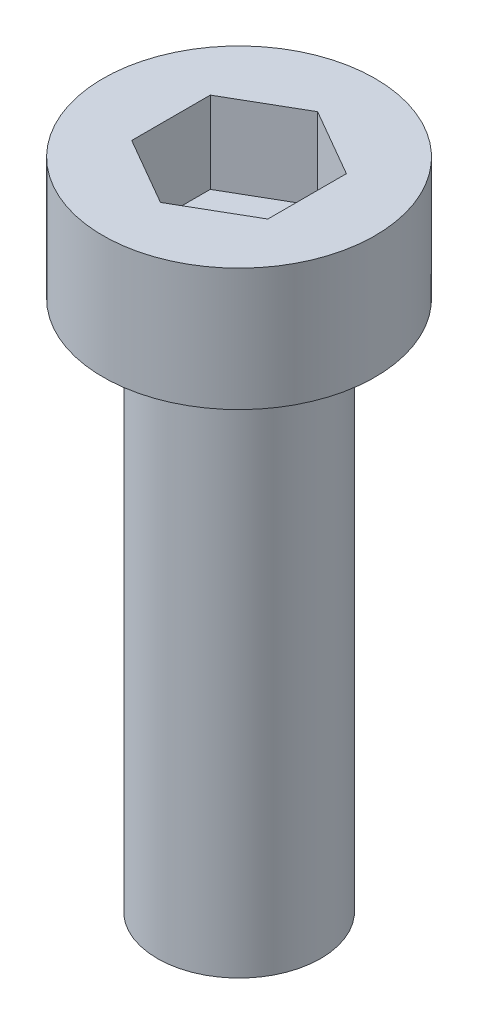
SolidWorks part; units mm, degrees
material "AISI 4340 Stal normalizowana"
ref_plane "Płaszczyzna XY" through (0, 0, 0) normal (0, 0, 1) x (1, 0, 0)
ref_plane "Płaszczyzna XZ" through (0, 0, 0) normal (0, 1, 0) x (1, 0, 0)
ref_plane "Płaszczyzna YZ" through (0, 0, 0) normal (1, 0, 0) x (0, 0, -1)
sketch "Szkic1" plane through (0, 0, 0) normal (0, 0, 1) x (1, 0, 0)
  line L0 (0, 0) -> (0, 9.2021) construction
  line L1 (0, 0) -> (5, 0)
  line L2 (5, 0) -> (5, -4.5)
  line L3 (5, -4.5) -> (3, -4.5)
  line L4 (3, -4.5) -> (3, -14.5)
  line L5 (3, -14.5) -> (3, -24)
  line L6 (3, -24) -> (2.5, -24)
  line L7 (2.5, -24) -> (0, -24)
  line L8 (0, 0) -> (0, -24)
  dimension "D1" = 3
  dimension "D2" = 2.5
  dimension "Leb sruby" = 4.5
  dimension "D3" = 0.5
  dimension "Dlugosc pasowana" = 10
  dimension "D4" = 2
  dimension "Srednica pasowana" = 6
revolve "Obrót1" add sketch "Szkic1" angle 360 about L0
sketch "Szkic2" plane through (0, 0, 0) normal (0, 1, 0) x (1, 0, 0)
  line L1 (0, 2.8868) -> (-2.5, 1.4434)
  line L2 (-2.5, 1.4434) -> (-2.5, -1.4434)
  line L3 (-2.5, -1.4434) -> (0, -2.8868)
  line L4 (0, -2.8868) -> (2.5, -1.4434)
  line L5 (2.5, -1.4434) -> (2.5, 1.4434)
  line L6 (2.5, 1.4434) -> (0, 2.8868)
  circle A0 centre (0, 0) radius 2.5 construction
  dimension "D1" = 5
extrude "Wytnij-wyciągnięcie1" cut sketch "Szkic2" against normal blind 3
